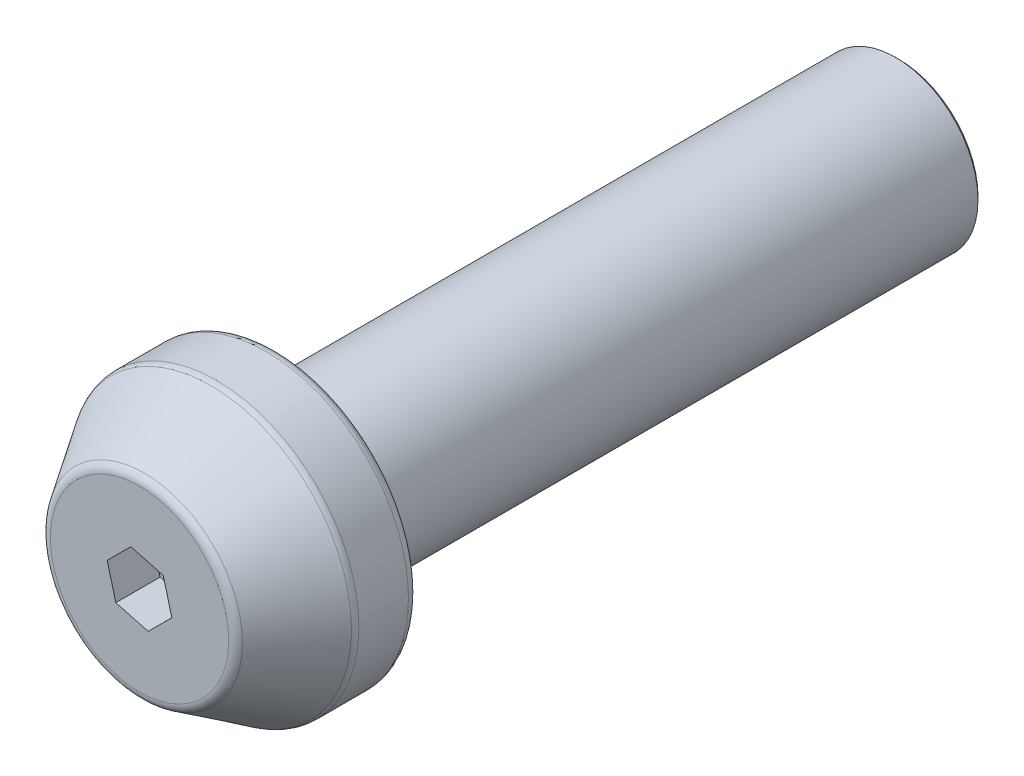
SolidWorks part; units mm, degrees
material "1.0037 (S235JR)"
ref_plane "Front Plane" through (0, 0, 0) normal (0, 0, 1) x (1, 0, 0)
ref_plane "Top Plane" through (0, 0, 0) normal (0, 1, 0) x (1, 0, 0)
ref_plane "Right Plane" through (0, 0, 0) normal (1, 0, 0) x (0, 0, -1)
sketch "Sketch1" plane through (0, 0, 0) normal (0, 0, 1) x (1, 0, 0)
  circle A0 centre (0, 0) radius 3.9
  dimension "D1" = 7.8
extrude "Boss-Extrude1" add sketch "Sketch1" along normal blind 29.5
sketch "Sketch2" plane through (0, 0, 29.5) normal (0, 0, 1) x (1, 0, 0)
  circle A0 centre (0, 0) radius 6.75
  dimension "D1" = 13.5
extrude "Boss-Extrude2" add sketch "Sketch2" along normal blind 3
ref_plane "Plane1" through (0, 0, 36) normal (0, 0, 1) x (1, 0, 0)
sketch "Sketch3" plane through (0, 0, 36) normal (0, 0, 1) x (1, 0, 0)
  circle A0 centre (0, 0) radius 4.5
  dimension "D1" = 9
loft "Loft1" add profiles "Sketch3" section edge at (6.75, 0, 32.5) section "Sketch3"
fillet "Fillet1" radius 0.5 3 edges at (4.5, 0, 36) (6.75, 0, 32.5) (6.75, 0, 29.5)
sketch "Sketch6" plane through (0, 0, 36) normal (0, 0, 1) x (1, 0, 0)
  line L1 (1.5332, -0.4123) -> (1.1237, 1.1217)
  line L2 (1.1237, 1.1217) -> (-0.4095, 1.534)
  line L3 (-0.4095, 1.534) -> (-1.5332, 0.4123)
  line L4 (-1.5332, 0.4123) -> (-1.1237, -1.1217)
  line L5 (-1.1237, -1.1217) -> (0.4095, -1.534)
  line L6 (0.4095, -1.534) -> (1.5332, -0.4123)
  circle A0 centre (0, 0) radius 1.375 construction
  dimension "D1" = 2.75
extrude "Cut-Extrude1" cut sketch "Sketch6" against normal blind 2.1
hole_wizard "M6 Tapped Hole1" positions "Sketch12" profile "Sketch11" tap size "M6" standard "ISO"
sketch "Sketch12" plane through (0, 0, 0) normal (0, 0, -1) x (-1, 0, 0)
  circle A0 centre (0, 0) radius 3.9 construction
  point P0 (0, 0)
sketch "Sketch11" plane through (0, 0, 0) normal (1, 0, 0) x (0, 1, 0)
  line L0 (0, 0) -> (0, 16.5022)
  line L1 (0, 16.5022) -> (2.5, 15)
  line L2 (2.5, 15) -> (2.5, 0)
  line L5 (2.5, 0) -> (0, 0)
  line L10 (0, 16.5022) -> (-2.5, 15) construction
  line L11 (0, -6.35) -> (0, 107.95) construction
  dimension "Tap Drill Dia." = 5
  dimension "Tap Drill Depth" = 15
  dimension "Drill Angle" = 118
cosmetic thread "Hole Thread2" parameters "D1"=12, "D2"=6
chamfer "Chamfer1" distance 0.15 angle 45 1 edges at (3.9, 0, 0)
